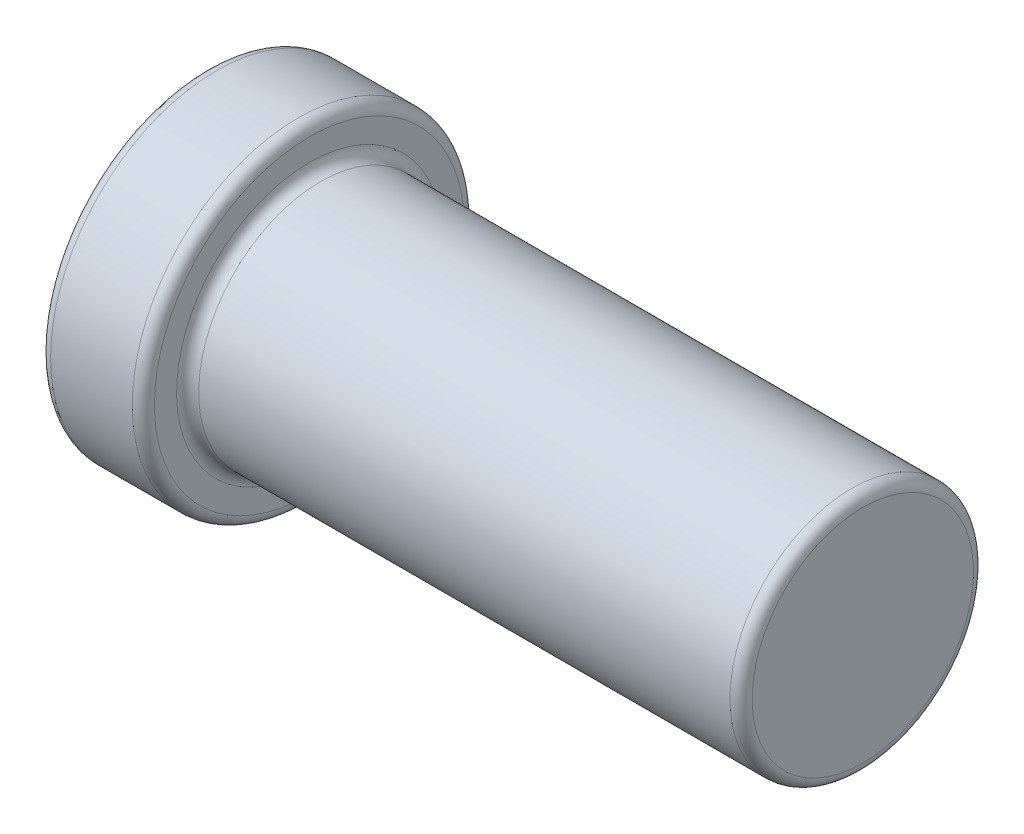
SolidWorks part; units mm, degrees
material "AISI 1035 Steel (SS)"
ref_plane "Front Plane" through (0, 0, 0) normal (0, 0, 1) x (1, 0, 0)
ref_plane "Top Plane" through (0, 0, 0) normal (0, 1, 0) x (1, 0, 0)
ref_plane "Right Plane" through (0, 0, 0) normal (1, 0, 0) x (0, 0, -1)
sketch "Sketch1" plane through (0, 0, 0) normal (0, 0, 1) x (1, 0, 0)
  line L1 (0, 1.5) -> (1, 1.5)
  line L2 (1, 1.5) -> (1, 1.1)
  line L3 (1, 1.1) -> (6, 1.1)
  line L4 (6, 1.1) -> (6, 0)
  line L5 (6, 0) -> (0.5, 0)
  line L7 (0.5, 0) -> (0.5, 0.5)
  line L8 (0.5, 0.5) -> (0, 1.5)
  dimension "D2" = 1
  dimension "D3" = 0.4
  dimension "D4" = 5
  dimension "D5" = 0.5
revolve "Revolve1" add sketch "Sketch1" angle 360 about L5
fillet "Fillet1" radius 0.1 1 edges at (6, 1.1, 0)
fillet "Fillet2" radius 0.1 4 edges at (1, 1.1, 0) (1, 1.5, 0) (0.5, 0.5, 0) (0, 1.5, 0)
